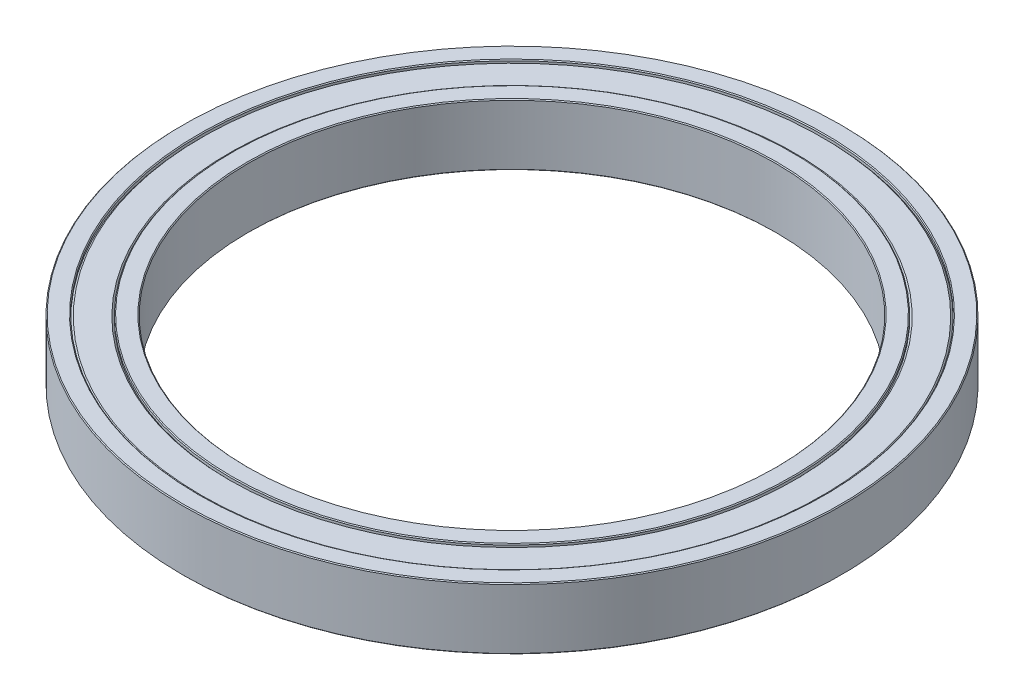
SolidWorks part; units mm, degrees
ref_plane "Front Plane" through (0, 0, 0) normal (0, 0, 1) x (1, 0, 0)
ref_plane "Top Plane" through (0, 0, 0) normal (0, 1, 0) x (1, 0, 0)
ref_plane "Right Plane" through (0, 0, 0) normal (1, 0, 0) x (0, 0, -1)
sketch "Sketch1" plane through (0, 0, 0) normal (1, 0, 0) x (0, 0, -1)
  line L1 (0, 3.5) -> (37.5, 3.5)
  line L2 (0, 3.5) -> (0, -3.5) construction
  line L3 (0, -3.5) -> (37.5, -3.5)
  line L4 (37.5, 3.5) -> (37.5, -3.5)
  line L6 (36.1, 0) -> (0, 0) construction
  line L7 (30, 3.5) -> (30, -3.5)
  dimension "D1" = 7
  dimension "D2" = 37.5
  dimension "D3" = 1.4
  dimension "D5" = 60
revolve "Revolve1" add sketch "Sketch1" angle 360 about L2
sketch "Sketch3" plane through (0, 0, 0) normal (1, 0, 0) x (0, 0, -1)
  line L0 (37.5, 3.5) -> (37.5, -3.5) construction
  line L1 (30, 3.5) -> (30, -3.5) construction
  line L2 (0, 3.5) -> (37.5, 3.5) construction
  line L3 (37.5, 3.5) -> (37.5, -3.5) construction
  line L4 (30, 3.5) -> (30, -3.5)
  line L5 (0, 3.5) -> (37.5, 3.5) construction
  line L6 (32, 3.5) -> (35.5, 3.5)
  line L7 (32, 3.5) -> (32, 3.1)
  line L8 (32, 3.1) -> (32.2, 3.3)
  line L9 (32.2, 3.3) -> (35.3, 3.3)
  line L10 (35.3, 3.3) -> (35.5, 3.1)
  line L11 (35.5, 3.1) -> (35.5, 3.5)
  line L14 (0, 3.5) -> (0, -3.5) construction
  line L17 (0, 3.5) -> (0, -3.5) construction
  line L18 (32, 3.1) -> (35.5, 3.1) construction
  line L19 (33.75, 3.1) -> (33.75, 3.5) construction
  dimension "D1" = 2
  dimension "D2" = 0.2
  dimension "D3" = 2
  dimension "D4" = 0.2
  dimension "D5" = 0.2
revolve "Cut-Revolve2" cut sketch "Sketch3" angle 360 about L17
mirror "Mirror1" about plane through (0, 0, 0) normal (0, 1, 0) of "Cut-Revolve2"
chamfer "Chamfer1" distance 0.1 angle 45 8 edges at (0, -3.5, 35.5) (0, 3.5, 35.5) (0, -3.5, 37.5) (0, 3.5, 37.5) (0, -3.5, 32) (0, 3.5, 32) (0, -3.5, 30) (0, 3.5, 30)
